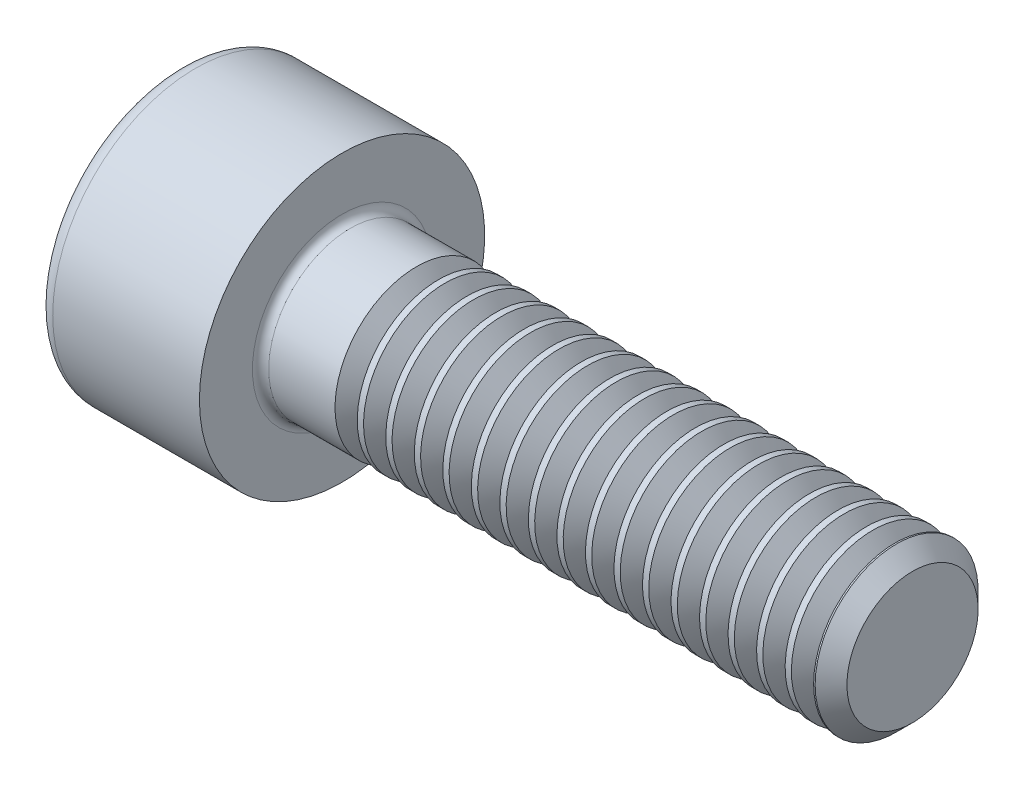
SolidWorks part; units mm, degrees
revolve "Base-Revolve" add sketch "BodySke"
sketch "BodySke" plane through (0, 0, 0) normal (0, 0, 1) x (1, 0, 0)
  line L0 (0, 0) -> (0, 3.5)
  line L1 (0, 3.5) -> (4, 3.5)
  line L2 (4, 3.5) -> (4, 2)
  line L3 (4, 2) -> (17.61, 2)
  line L4 (18, 1.61) -> (18, 0)
  line L5 (18, 0) -> (0, 0)
  line L6 (-31.75, 0) -> (127, 0) construction
  line L8 (18, 1.61) -> (17.61, 2)
  line L10 (18, -1.61) -> (17.61, -2) construction
  line L11 (4.7, 9.525) -> (4.7, 3.175) construction
  line L12 (4, 9.525) -> (4, 3.175) construction
  line L13 (-42, 9.525) -> (-42, 3.175) construction
cosmetic thread "ThreadCosmetic" [suppressed]
fillet "Fillet1" radius 0.2 1 edges at (4, 0, 2)
fillet "Fillet2" radius 0.4 1 edges at (0, 0, 3.5)
ref_plane "Plane1" through (0, 0, 0) normal (0, 0, 1) x (1, 0, 0)
ref_plane "Plane2" through (0, 0, 0) normal (0, 1, 0) x (1, 0, 0)
ref_plane "Plane3" through (0, 0, 0) normal (1, 0, 0) x (0, 0, -1)
sketch "Sketch2" plane through (0, 0, 0) normal (0, 0, 1) x (1, 0, 0)
  line L0 (0, 1.51) -> (2, 1.51)
  line L1 (2, 1.51) -> (2.8718, 0)
  line L2 (-31.75, 0) -> (127, 0) construction
  line L3 (2.8718, 0) -> (0, 0)
  line L4 (0, 0) -> (0, 1.51)
  line L6 (0, 0) -> (47.625, 0) construction
revolve "Hex-PreBroach" cut sketch "Sketch2" angle 360 about L6
sketch "Sketch3" plane through (0, 0, 0) normal (-1, 0, 0) x (0, 0.5, 0.866)
  line L0 (0.8718, 1.51) -> (-0.8718, 1.51)
  line L1 (-0.8718, 1.51) -> (-1.7436, 0)
  line L2 (0.8718, 1.51) -> (1.7436, 0)
  line L3 (0.8718, -1.51) -> (1.7436, 0)
  line L4 (0.8718, -1.51) -> (-0.8718, -1.51)
  line L5 (-0.8718, -1.51) -> (-1.7436, 0)
extrude "Hex" cut sketch "Sketch3" against normal blind 2
sketch "ThdSchSke" plane through (0, 0, 0) normal (0, 0, 1) x (1, 0, 0)
  line L0 (6.1, -1.61) -> (5.8269, -2)
  line L1 (6.1, -1.61) -> (6.3731, -2)
  line L2 (6.3731, -2) -> (6.3731, -2.5)
  line L3 (-3.175, 0) -> (5.1513, 0) construction
  line L4 (0, 3.1) -> (0, -3.1) construction
  line L5 (6.3731, -2.5) -> (5.8269, -2.5)
  line L6 (5.8269, -2.5) -> (5.8269, -2)
revolve "ThreadSchematic" cut sketch "ThdSchSke" angle 360 about L3
pattern_linear "ThdSchPat" count 17 spacing 0.7 along (1, 0, 0) of "ThreadSchematic"
equation "\"D2@Sketch3\" = \"Hex_size@Sketch3\" / 2"
equation "\"D1@Sketch3\" = \"Hex_size@Sketch3\" / 2"
equation "\"D1@Sketch2\" = \"Hex_size@Sketch3\" / 2"
equation "\"Thread_minor@ThreadCosmetic\"  =  \"Minor_dia@BodySke\""
equation "\"Depth@Sketch2\" =  \"Key_eng@Hex\""
equation "\"Thread_length@ThreadCosmetic\" = ((sgn( (\"Length@BodySke\" - \"Advance@BodySke\" * 3.0) - \"Thread_nom@BodySke\" )-1)*( (\"Length@BodySke\" - \"Advance@BodySke\" * 3.0) - \"Thread_nom@BodySke\" ))/-2+ \"Thread_nom@BodySke\""
equation "\"Thread_minor@ThdSchSke\" = \"Minor_dia@BodySke\""
equation "\"Diameter@ThdSchSke\" = \"Diameter@BodySke\""
equation "\"Overcut@ThdSchSke\" = \"Diameter@BodySke\" * 1.25"
equation "\"Start@ThdSchSke\" = \"Head_ht@BodySke\" + \"Length@BodySke\" - \"Thread_length@ThreadCosmetic\"  '---Non-countersunk---"
equation "\"Num_threads@ThdSchPat\" = int( \"Thread_length@ThreadCosmetic\" / \"Advance@BodySke\" + 0.999 )  + 1"
equation "\"Advance@ThdSchPat\" = \"Thread_length@ThreadCosmetic\" /  (\"Num_threads@ThdSchPat\" - 1) 'relax it"
equation "\"Num_threads@ThdSchPat\" = \"Num_threads@ThdSchPat\" - sgn( \"Num_threads@ThdSchPat\" - 1) '---chamfered tips only---"
